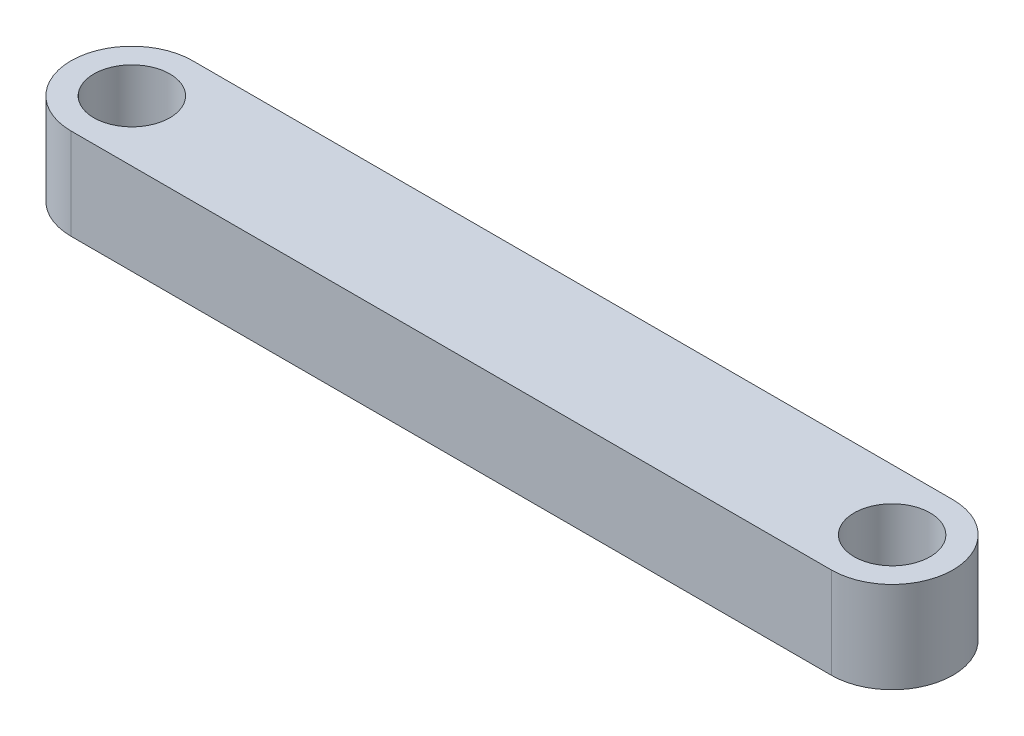
SolidWorks part; units mm, degrees
ref_plane "Front Plane" through (0, 0, 0) normal (0, 0, 1) x (1, 0, 0)
ref_plane "Top Plane" through (0, 0, 0) normal (0, 1, 0) x (1, 0, 0)
ref_plane "Right Plane" through (0, 0, 0) normal (1, 0, 0) x (0, 0, -1)
sketch "Sketch1" plane through (0, 0, 0) normal (0, 1, 0) x (1, 0, 0)
  line L0 (0, 0) -> (63.5, 0) construction
  line L1 (0, 5.08) -> (63.5, 5.08)
  line L2 (0, -5.08) -> (63.5, -5.08)
  circle A0 centre (0, 0) radius 3.175
  arc A1 (0, 5.08) -> (0, -5.08) centre (0, 0) ccw
  arc A2 (63.5, -5.08) -> (63.5, 5.08) centre (63.5, 0) ccw
  circle A3 centre (63.5, 0) radius 3.175
  point P3 (31.75, 0)
  dimension "D1" = 6.35
  dimension "D2" = 5.08
  dimension "D3" = 63.5
extrude "Boss-Extrude1" add sketch "Sketch1" along normal blind 7.62
